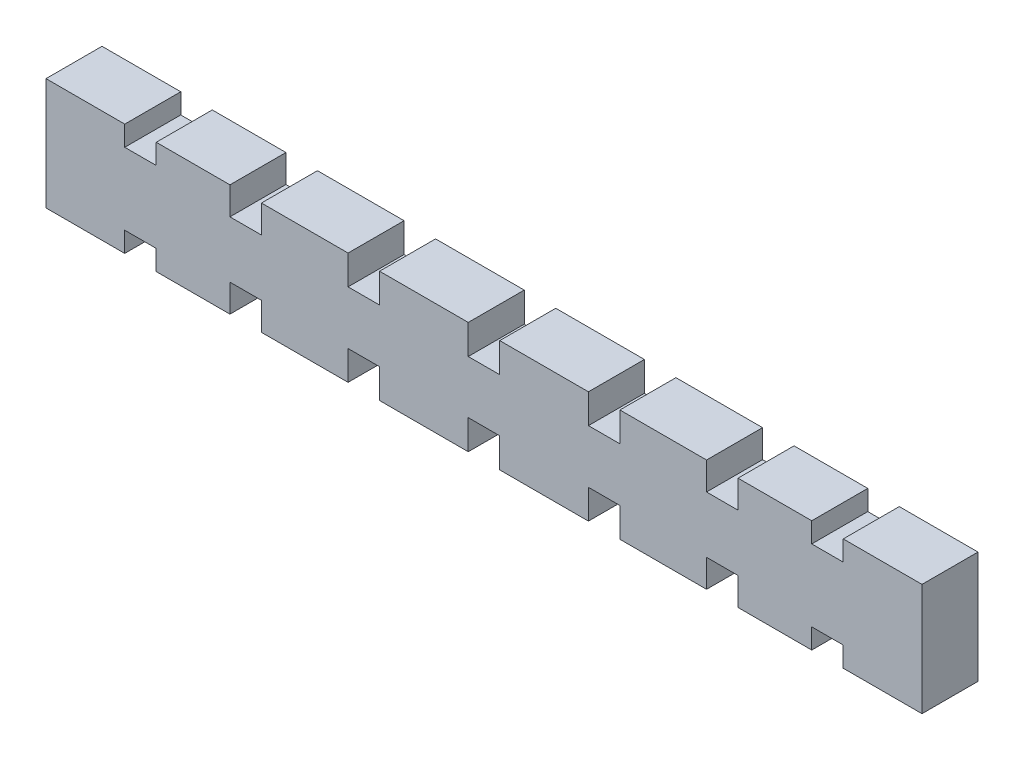
SolidWorks part; units mm, degrees
ref_plane "Top Plane" through (0, 0, 0) normal (0, 0, 1) x (1, 0, 0)
ref_plane "Right Plane" through (0, 0, 0) normal (0, 1, 0) x (1, 0, 0)
ref_plane "Front Plane" through (0, 0, 0) normal (1, 0, 0) x (0, 0, -1)
sketch "Sketch1" plane through (0, 0, 0) normal (0, 0, 1) x (1, 0, 0)
  line L0 (0, 0) -> (0, 1.68) construction
  line L1 (0, 0) -> (27.81, 0) construction
  line L2 (27.81, -3.556) -> (27.81, 3.556)
  line L3 (27.81, 3.556) -> (22.81, 3.556)
  line L4 (22.81, 3.556) -> (22.81, 2.28)
  line L5 (22.81, 2.28) -> (20.81, 2.28)
  line L6 (20.81, 2.28) -> (20.81, 3.556)
  line L7 (20.81, 3.556) -> (16.13, 3.556)
  line L8 (16.13, 3.556) -> (16.13, 1.795)
  line L9 (16.13, 1.795) -> (14.13, 1.795)
  line L10 (14.13, 1.795) -> (14.13, 3.556)
  line L11 (14.13, 3.556) -> (8.63, 3.556)
  line L12 (8.63, 3.556) -> (8.63, 1.695)
  line L13 (8.63, 1.695) -> (6.63, 1.695)
  line L14 (6.63, 1.695) -> (6.63, 3.556)
  line L15 (6.63, 3.556) -> (1, 3.556)
  line L16 (1, 3.556) -> (1, 1.68)
  line L17 (1, 1.68) -> (-1, 1.68)
  line L18 (-27.81, -3.556) -> (-27.81, 3.556)
  line L19 (-1, 3.556) -> (-1, 1.68)
  line L20 (-6.63, 3.556) -> (-1, 3.556)
  line L21 (-6.63, 1.695) -> (-6.63, 3.556)
  line L22 (-8.63, 1.695) -> (-6.63, 1.695)
  line L23 (-8.63, 3.556) -> (-8.63, 1.695)
  line L24 (-14.13, 3.556) -> (-8.63, 3.556)
  line L25 (-14.13, 1.795) -> (-14.13, 3.556)
  line L26 (-16.13, 1.795) -> (-14.13, 1.795)
  line L27 (-16.13, 3.556) -> (-16.13, 1.795)
  line L28 (-20.81, 3.556) -> (-16.13, 3.556)
  line L29 (-20.81, 2.28) -> (-20.81, 3.556)
  line L30 (-22.81, 2.28) -> (-20.81, 2.28)
  line L31 (-22.81, 3.556) -> (-22.81, 2.28)
  line L32 (-27.81, 3.556) -> (-22.81, 3.556)
  line L33 (-27.81, -3.556) -> (-22.81, -3.556)
  line L34 (-22.81, -3.556) -> (-22.81, -2.28)
  line L35 (-22.81, -2.28) -> (-20.81, -2.28)
  line L36 (-20.81, -2.28) -> (-20.81, -3.556)
  line L37 (-20.81, -3.556) -> (-16.13, -3.556)
  line L38 (-16.13, -3.556) -> (-16.13, -1.795)
  line L39 (-16.13, -1.795) -> (-14.13, -1.795)
  line L40 (-14.13, -1.795) -> (-14.13, -3.556)
  line L41 (-14.13, -3.556) -> (-8.63, -3.556)
  line L42 (-8.63, -3.556) -> (-8.63, -1.695)
  line L43 (-8.63, -1.695) -> (-6.63, -1.695)
  line L44 (-6.63, -1.695) -> (-6.63, -3.556)
  line L45 (-6.63, -3.556) -> (-1, -3.556)
  line L46 (-1, -3.556) -> (-1, -1.68)
  line L47 (1, -1.68) -> (-1, -1.68)
  line L48 (1, -3.556) -> (1, -1.68)
  line L49 (6.63, -3.556) -> (1, -3.556)
  line L50 (6.63, -1.695) -> (6.63, -3.556)
  line L51 (8.63, -1.695) -> (6.63, -1.695)
  line L52 (8.63, -3.556) -> (8.63, -1.695)
  line L53 (14.13, -3.556) -> (8.63, -3.556)
  line L54 (14.13, -1.795) -> (14.13, -3.556)
  line L55 (16.13, -1.795) -> (14.13, -1.795)
  line L56 (16.13, -3.556) -> (16.13, -1.795)
  line L57 (20.81, -3.556) -> (16.13, -3.556)
  line L58 (20.81, -2.28) -> (20.81, -3.556)
  line L59 (22.81, -2.28) -> (20.81, -2.28)
  line L60 (22.81, -3.556) -> (22.81, -2.28)
  line L61 (27.81, -3.556) -> (22.81, -3.556)
  point P50 (-27.81, 0)
  dimension "D1" = 2
  dimension "D2" = 5
  dimension "D3" = 4.68
  dimension "D4" = 5.5
  dimension "D5" = 5.63
  dimension "D6" = 7.112
  dimension "D7" = 4.56
  dimension "D8" = 3.59
  dimension "D9" = 3.39
  dimension "D10" = 3.36
extrude "Boss-Extrude1" add sketch "Sketch1" along normal blind 3.556
